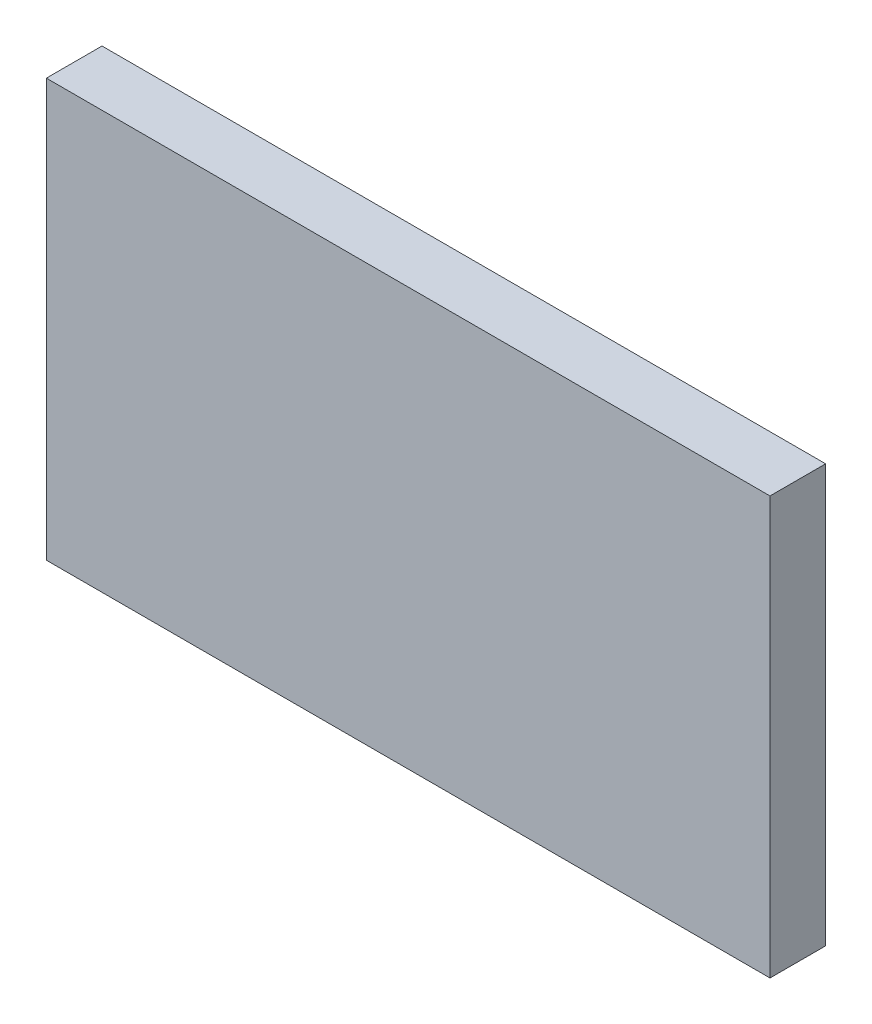
SolidWorks part; units mm, degrees
ref_plane "Front Plane" through (0, 0, 0) normal (0, 0, 1) x (1, 0, 0)
ref_plane "Top Plane" through (0, 0, 0) normal (0, 1, 0) x (1, 0, 0)
ref_plane "Right Plane" through (0, 0, 0) normal (1, 0, 0) x (0, 0, -1)
sketch "Sketch1" plane through (0, 0, 0) normal (0, 1, 0) x (1, 0, 0)
  line L1 (0, 0) -> (-130, 0)
  line L2 (0, 0) -> (0, 10)
  line L3 (0, 10) -> (-130, 10)
  line L4 (-130, 0) -> (-130, 10)
  dimension "D1" = 130
  dimension "D2" = 10
extrude "Boss-Extrude1" add sketch "Sketch1" along normal blind 75
